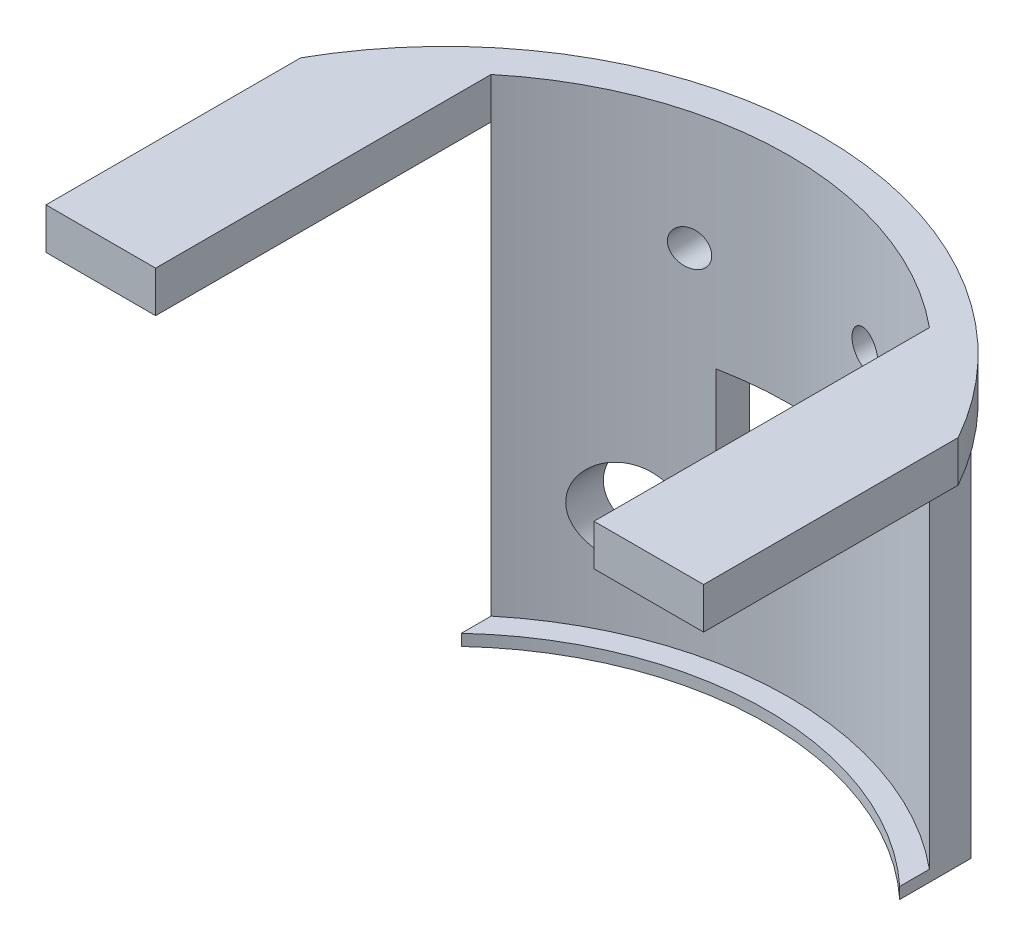
SolidWorks part; units mm, degrees
ref_plane "Front Plane" through (0, 0, 0) normal (0, 0, 1) x (1, 0, 0)
ref_plane "Top Plane" through (0, 0, 0) normal (0, 1, 0) x (1, 0, 0)
ref_plane "Right Plane" through (0, 0, 0) normal (1, 0, 0) x (0, 0, -1)
sketch "Sketch2" plane through (0, 0, 0) normal (0, 1, 0) x (1, 0, 0)
  line L0 (-37.5, 21.0416) -> (-37.5, -8)
  line L1 (-37.5, -8) -> (37.5, -8)
  line L2 (37.5, -8) -> (37.5, 21.0416)
  line L3 (0, 43) -> (0, 0) construction
  arc A0 (37.5, 21.0416) -> (-37.5, 21.0416) centre (0, 0) ccw
  dimension "D1" = 86
  dimension "D3" = 51
  dimension "D4" = 75
extrude "Boss-Extrude1" add sketch "Sketch2" along normal blind 54.8
sketch "Sketch3" plane through (0, 54.8, 0) normal (0, 1, 0) x (1, 0, 0)
  line L1 (-37.5, 21.0416) -> (-37.5, -8) construction
  line L4 (37.5, -8) -> (37.5, 21.0416) construction
  line L5 (-25, 30.2583) -> (-25, -8)
  line L6 (-37.5, -8) -> (37.5, -8) construction
  line L7 (-25, -8) -> (25, -8)
  line L8 (25, -8) -> (25, 30.2583)
  arc A1 (37.5, 21.0416) -> (-37.5, 21.0416) centre (0, 0) ccw construction
  arc A2 (25, 30.2583) -> (-25, 30.2583) centre (0, 0) ccw
  point P2 (0, 0)
  dimension "D1" = 78.5
  dimension "D4" = 3.75
  dimension "D2" = 12.5
  dimension "D3" = 12.5
extrude "Cut-Extrude1" cut sketch "Sketch3" against normal blind 53.5
sketch "Sketch4" plane through (0, 0, 0) normal (0, -1, 0) x (1, 0, 0)
  line L7 (25, 8) -> (25, -34.9857)
  line L8 (-37.5, 8) -> (37.5, 8) construction
  line L9 (-25, 8) -> (-25, -34.9857)
  line L10 (25, 8) -> (37.5, 8)
  line L11 (37.5, 8) -> (37.5, -21.0416)
  line L12 (-37.5, -21.0416) -> (-37.5, 8)
  line L13 (-37.5, 8) -> (-25, 8)
  arc A2 (25, -34.9857) -> (37.5, -21.0416) centre (0, 0) ccw
  arc A4 (-37.5, -21.0416) -> (-25, -34.9857) centre (0, 0) ccw
  dimension "D1" = 50
  dimension "D2" = 12.5
  dimension "D3" = 12.5
extrude "Cut-Extrude2" cut sketch "Sketch4" against normal blind 50.1
sketch "Sketch5" plane through (0, 0, 8) normal (0, 0, 1) x (1, 0, 0)
  line L0 (0, 0) -> (0, 63.3579) construction
  line L1 (-7.6, 30.3) -> (7.6, 30.3)
  line L2 (-7.6, 30.3) -> (-7.6, 21.3)
  line L3 (-7.6, 21.3) -> (7.6, 21.3)
  line L4 (7.6, 30.3) -> (7.6, 21.3)
  line L5 (-25, 1.3) -> (25, 1.3) construction
  line L6 (-25, 0) -> (25, 0) construction
  line L8 (-25, 1.3) -> (-25, 50.1) construction
  circle A0 centre (-10, 41.3) radius 2
  circle A1 centre (10, 41.3) radius 2
  circle A2 centre (-15, 13.3) radius 5
  point P12 (0, 30.3)
  point P15 (0, 0)
  dimension "D1" = 4
  dimension "D2" = 20
  dimension "D7" = 10
  dimension "D8" = 8
  dimension "D9" = 10
  dimension "D3" = 40
  dimension "D4" = 15.2
  dimension "D5" = 9
  dimension "D6" = 20
extrude "Cut-Extrude4" cut sketch "Sketch5" against normal up to surface (50.323 mm away)
sketch "Sketch6" plane through (0, 1.3, 0) normal (0, 1, 0) x (1, 0, 0)
  circle A0 centre (0, 0) radius 36.7
extrude "Cut-Extrude5" cut sketch "Sketch6" against normal blind 10
